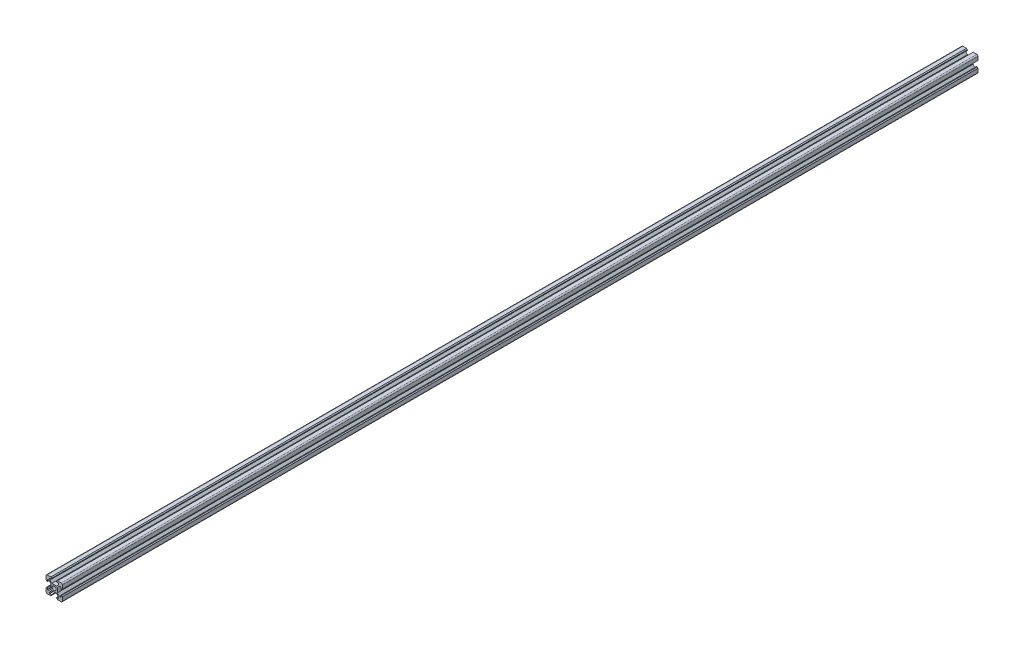
SolidWorks part; units mm, degrees
ref_plane "Front Plane" through (0, 0, 0) normal (0, 0, 1) x (1, 0, 0)
ref_plane "Top Plane" through (0, 0, 0) normal (0, 1, 0) x (1, 0, 0)
ref_plane "Right Plane" through (0, 0, 0) normal (1, 0, 0) x (0, 0, -1)
sketch "Sketch1" plane through (0, 0, 0) normal (0, 0, 1) x (1, 0, 0)
  line L0 (0, 16.1631) -> (0, -12.0251) construction
  line L1 (-21.8377, 0) -> (16.3885, 0) construction
  line L2 (2.8393, 3.9) -> (-2.8393, 3.9)
  line L3 (-2.8393, 3.9) -> (-5.5, 6.5607)
  line L4 (-5.5, 6.5607) -> (-5.5, 8.2)
  line L5 (-5.5, 8.2) -> (-3.1, 8.2)
  line L6 (-3.1, 8.2) -> (-3.1, 9)
  line L7 (-4.1, 10) -> (-8.5, 10)
  line L8 (-10, 8.5) -> (-10, 4.1)
  line L9 (-9, 3.1) -> (-8.2, 3.1)
  line L10 (-8.2, 3.1) -> (-8.2, 5.5)
  line L11 (-8.2, 5.5) -> (-6.5607, 5.5)
  line L12 (-6.5607, 5.5) -> (-3.9, 2.8393)
  line L13 (-3.9, 2.8393) -> (-3.9, -2.8393)
  line L14 (11.4015, -11.4015) -> (-14.8602, 14.8602) construction
  line L15 (-3.1, 9) -> (-4.1, 10)
  line L16 (-10, 4.1) -> (-9, 3.1)
  line L17 (-10, -4.1) -> (-9, -3.1)
  line L18 (-3.1, -9) -> (-4.1, -10)
  line L19 (-6.5607, -5.5) -> (-3.9, -2.8393)
  line L20 (-8.2, -5.5) -> (-6.5607, -5.5)
  line L21 (-8.2, -3.1) -> (-8.2, -5.5)
  line L22 (-9, -3.1) -> (-8.2, -3.1)
  line L23 (-10, -8.5) -> (-10, -4.1)
  line L24 (-4.1, -10) -> (-8.5, -10)
  line L25 (-3.1, -8.2) -> (-3.1, -9)
  line L26 (-5.5, -8.2) -> (-3.1, -8.2)
  line L27 (-5.5, -6.5607) -> (-5.5, -8.2)
  line L28 (-2.8393, -3.9) -> (-5.5, -6.5607)
  line L29 (2.8393, -3.9) -> (-2.8393, -3.9)
  line L30 (2.8393, -3.9) -> (5.5, -6.5607)
  line L31 (5.5, -6.5607) -> (5.5, -8.2)
  line L32 (5.5, -8.2) -> (3.1, -8.2)
  line L33 (3.1, -8.2) -> (3.1, -9)
  line L34 (4.1, -10) -> (8.5, -10)
  line L35 (10, -8.5) -> (10, -4.1)
  line L36 (9, -3.1) -> (8.2, -3.1)
  line L37 (8.2, -3.1) -> (8.2, -5.5)
  line L38 (8.2, -5.5) -> (6.5607, -5.5)
  line L39 (6.5607, -5.5) -> (3.9, -2.8393)
  line L40 (3.1, -9) -> (4.1, -10)
  line L41 (10, -4.1) -> (9, -3.1)
  line L42 (10, 4.1) -> (9, 3.1)
  line L43 (3.1, 9) -> (4.1, 10)
  line L44 (3.9, 2.8393) -> (3.9, -2.8393)
  line L45 (6.5607, 5.5) -> (3.9, 2.8393)
  line L46 (8.2, 5.5) -> (6.5607, 5.5)
  line L47 (8.2, 3.1) -> (8.2, 5.5)
  line L48 (9, 3.1) -> (8.2, 3.1)
  line L49 (10, 8.5) -> (10, 4.1)
  line L50 (4.1, 10) -> (8.5, 10)
  line L51 (3.1, 8.2) -> (3.1, 9)
  line L52 (5.5, 8.2) -> (3.1, 8.2)
  line L53 (5.5, 6.5607) -> (5.5, 8.2)
  line L54 (2.8393, 3.9) -> (5.5, 6.5607)
  circle A0 centre (0, 0) radius 2.5
  arc A1 (-10, 8.5) -> (-8.5, 10) centre (-8.5, 8.5) cw
  arc A2 (-10, -8.5) -> (-8.5, -10) centre (-8.5, -8.5) ccw
  arc A3 (10, -8.5) -> (8.5, -10) centre (8.5, -8.5) cw
  arc A4 (10, 8.5) -> (8.5, 10) centre (8.5, 8.5) ccw
  point P7 (3.1, -10)
  point P13 (-3.1, 10)
  point P15 (-10, 3.1)
  point P36 (-3.9, 0)
  point P44 (-10, -3.1)
  point P45 (-3.1, -10)
  point P53 (0, -3.9)
  point P76 (0, 3.9)
  point P77 (10, -3.1)
  point P78 (3.9, 0)
  point P79 (10, 3.1)
  point P80 (3.1, 10)
  dimension "D1" = 5
  dimension "D11" = 1.5
  dimension "D2" = 45
  dimension "D3" = 3.9
  dimension "D4" = 3.9
  dimension "D5" = 1.5
  dimension "D6" = 10
  dimension "D7" = 10
  dimension "D8" = 3.1
  dimension "D9" = 4.3
  dimension "D10" = 5.5
extrude "Boss-Extrude1" add sketch "Sketch1" along normal blind 1120
